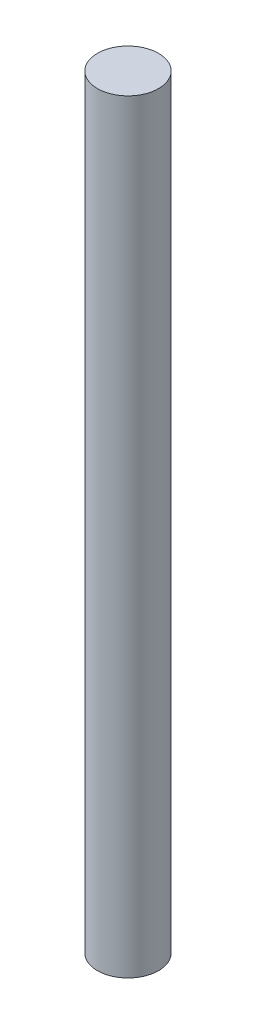
SolidWorks part; units mm, degrees
ref_plane "前视基准面" through (0, 0, 0) normal (0, 0, 1) x (1, 0, 0)
ref_plane "上视基准面" through (0, 0, 0) normal (0, 1, 0) x (1, 0, 0)
ref_plane "右视基准面" through (0, 0, 0) normal (1, 0, 0) x (0, 0, -1)
sketch "Sketch1" plane through (0, 0, 0) normal (0, 1, 0) x (1, 0, 0)
  circle A0 centre (0, 0) radius 4
  dimension "D1" = 8
extrude "Boss-Extrude1" add sketch "Sketch1" along normal blind 100
